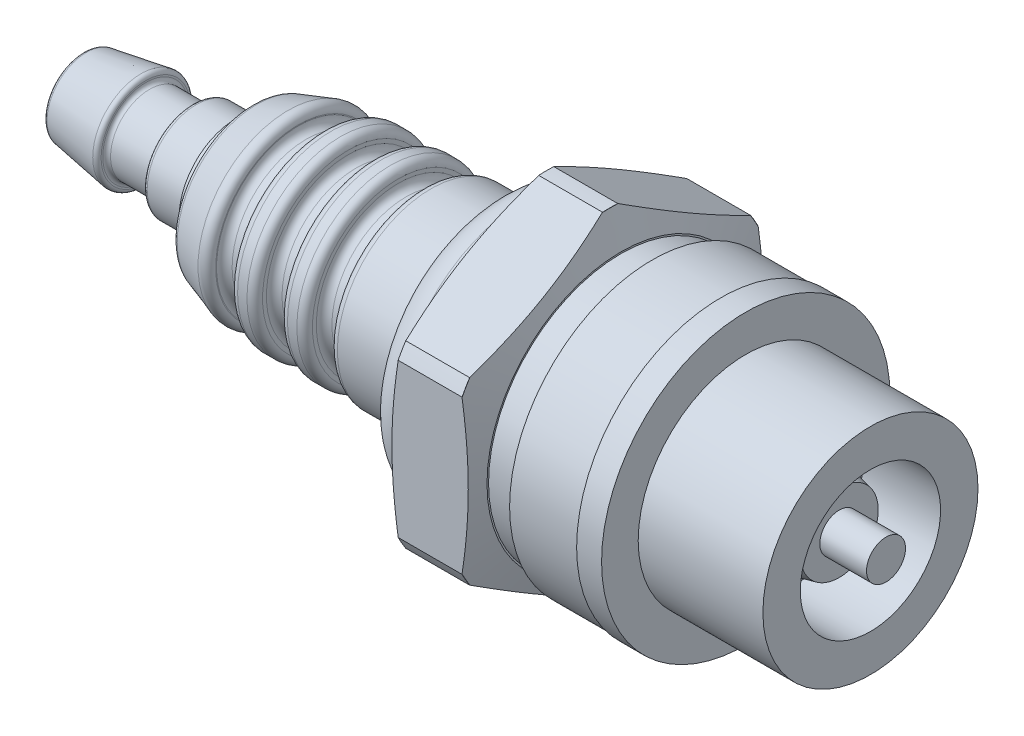
SolidWorks part; units mm, degrees
material "Stainless Steel (ferritic)"
ref_plane "Front Plane" through (0, 0, 0) normal (0, 0, 1) x (1, 0, 0)
ref_plane "Top Plane" through (0, 0, 0) normal (0, 1, 0) x (1, 0, 0)
ref_plane "Right Plane" through (0, 0, 0) normal (1, 0, 0) x (0, 0, -1)
sketch "Sketch1" plane through (0, 0, 0) normal (0, 0, 1) x (1, 0, 0)
  line L0 (0, 0) -> (51.5, 0) construction
  line L1 (2, 0) -> (2, 1.65)
  line L2 (2, 1.65) -> (0, 1.65)
  line L3 (0, 1.65) -> (0, 2.5)
  line L4 (0, 2.5) -> (4, 3.15)
  line L5 (4, 3.15) -> (4, 2.5)
  line L6 (4, 2.5) -> (7, 2.5)
  line L7 (7, 2.5) -> (7, 3.15)
  line L8 (7, 3.15) -> (9.8, 3.15)
  line L9 (9.8, 3.15) -> (9.8, 3.65)
  line L10 (9.8, 3.65) -> (10.8, 3.65)
  line L11 (10.8, 3.65) -> (10.8, 5)
  line L12 (10.8, 5) -> (13.8, 6)
  line L13 (13.8, 6) -> (26.5, 6)
  line L14 (26.5, 6) -> (26.5, 8.6)
  line L15 (26.5, 8.6) -> (29, 8.6)
  line L16 (29, 8.6) -> (29, 10.7)
  line L17 (29, 10.7) -> (34.5, 10.7)
  line L18 (34.5, 10.7) -> (34.5, 8.5)
  line L19 (34.5, 8.5) -> (36.5, 8.5)
  line L20 (36.5, 8.5) -> (36.5, 9.15)
  line L21 (36.5, 9.15) -> (40.9, 9.15)
  line L22 (40.9, 9.15) -> (40.9, 9.25)
  line L23 (40.9, 9.25) -> (42.5, 9.25)
  line L24 (42.5, 9.25) -> (42.5, 6.9)
  line L25 (42.5, 6.9) -> (50.5, 6.9)
  line L26 (50.5, 6.9) -> (50.5, 4.5)
  line L27 (50.5, 4.5) -> (45.5, 4.5)
  line L28 (45.5, 4.5) -> (45.5, 3.15)
  line L29 (45.5, 3.15) -> (48.5, 2.5)
  line L30 (48.5, 2.5) -> (48.5, 1.25)
  line L31 (48.5, 1.25) -> (51.5, 1.25)
  line L32 (51.5, 1.25) -> (51.5, 0)
  line L33 (51.5, 0) -> (2, 0)
  dimension "D1" = 3.3
  dimension "D2" = 5
  dimension "D3" = 5
  dimension "D4" = 6.3
  dimension "D5" = 7.3
  dimension "D6" = 10
  dimension "D7" = 12
  dimension "D8" = 17.2
  dimension "D9" = 21.4
  dimension "D10" = 17
  dimension "D11" = 18.3
  dimension "D12" = 18.5
  dimension "D13" = 13.8
  dimension "D14" = 9
  dimension "D15" = 2.5
  dimension "D16" = 4
  dimension "D17" = 2
  dimension "D18" = 7
  dimension "D19" = 9.8
  dimension "D20" = 10.8
  dimension "D21" = 3
  dimension "D22" = 15.7
  dimension "D23" = 2.5
  dimension "D24" = 5.5
  dimension "D25" = 2
  dimension "D26" = 4.4
  dimension "D27" = 8
  dimension "D28" = 8
  dimension "D29" = 5
  dimension "D30" = 5
  dimension "D31" = 2
  dimension "D32" = 1
revolve "Revolve1" add sketch "Sketch1" angle 360 about L0
sketch "Sketch2" plane through (34.5, 0, 0) normal (1, 0, 0) x (0, 0, -1)
  line L1 (0, 10.9697) -> (-9.5, 5.4848)
  line L2 (-9.5, 5.4848) -> (-9.5, -5.4848)
  line L3 (-9.5, -5.4848) -> (0, -10.9697)
  line L4 (0, -10.9697) -> (9.5, -5.4848)
  line L5 (9.5, -5.4848) -> (9.5, 5.4848)
  line L6 (9.5, 5.4848) -> (0, 10.9697)
  circle A0 centre (0, 0) radius 9.5 construction
  circle A1 centre (0, 0) radius 12.6266
  dimension "D1" = 19
extrude "Cut-Extrude1" cut sketch "Sketch2" against normal blind 10
sketch "Sketch3" plane through (0, 0, 0) normal (0, 0, 1) x (1, 0, 0)
  line L0 (13.8, 6) -> (13.8, -6) construction
  line L1 (13.8, 4.75) -> (15.4, 4.75)
  line L2 (13.8, 4.75) -> (13.8, 7.215)
  line L3 (13.8, 7.215) -> (15.4, 7.215)
  line L4 (15.4, 4.75) -> (15.4, 7.215)
  line L5 (0, 0) -> (48.9499, 0) construction
  line L6 (17, 4.75) -> (18.6, 4.75)
  line L7 (17, 4.75) -> (17, 7.1135)
  line L8 (17, 7.1135) -> (18.6, 7.1135)
  line L9 (18.6, 4.75) -> (18.6, 7.1135)
  line L10 (20.2, 4.75) -> (21.8, 4.75)
  line L11 (20.2, 4.75) -> (20.2, 7.1135)
  line L12 (20.2, 7.1135) -> (21.8, 7.1135)
  line L13 (21.8, 4.75) -> (21.8, 7.1135)
  line L14 (29, 10.6889) -> (29, 8.6)
  line L15 (29, 8.6) -> (29.7, 10.6889)
  line L16 (34.5, 10.6889) -> (29, 10.6889) construction
  line L18 (31.75, 10.6889) -> (31.75, 7.6353) construction
  line L20 (34.5, 8.6) -> (33.8, 10.6889)
  line L21 (34.5, 10.6889) -> (34.5, 8.6)
  line L24 (29, 10.6889) -> (29, 11.9244)
  line L25 (29, 11.9244) -> (29.7, 11.9244)
  line L26 (29.7, 10.6889) -> (29.7, 11.9244)
  line L32 (33.8, 10.6889) -> (33.8, 13.1642)
  line L33 (33.8, 13.1642) -> (34.5, 13.1642)
  line L34 (34.5, 10.6889) -> (34.5, 13.1642)
  dimension "D1" = 1.6
  dimension "D2" = 1.6
  dimension "D3" = 1.6
  dimension "D4" = 9.5
  dimension "D5" = 1.6
  dimension "D6" = 1.6
  dimension "D7" = 0.7
revolve "Cut-Revolve1" cut sketch "Sketch3" angle 360 about L5
fillet "Fillet1" radius 0.5 13 edges at (20.2, 0, 4.75) (21.8, 0, 4.75) (17, 0, 4.75) (18.6, 0, 4.75) (13.8, 0, 4.75) (15.4, 0, 4.75) (20.2, 0, -6) (18.6, 0, 6) (17, 0, -6) (15.4, 0, 6) (10.8, 0, 5) (21.8, 0, 6) (13.8, 0, -6)
fillet "Fillet2" radius 0.25 5 edges at (4, 0, 3.15) (0, 0, 2.5) (7, 0, 2.5) (4, 0, 2.5) (7, 0, 3.15)
fillet "Fillet3" radius 2 1 edges at (26.5, 0, 8.6)
